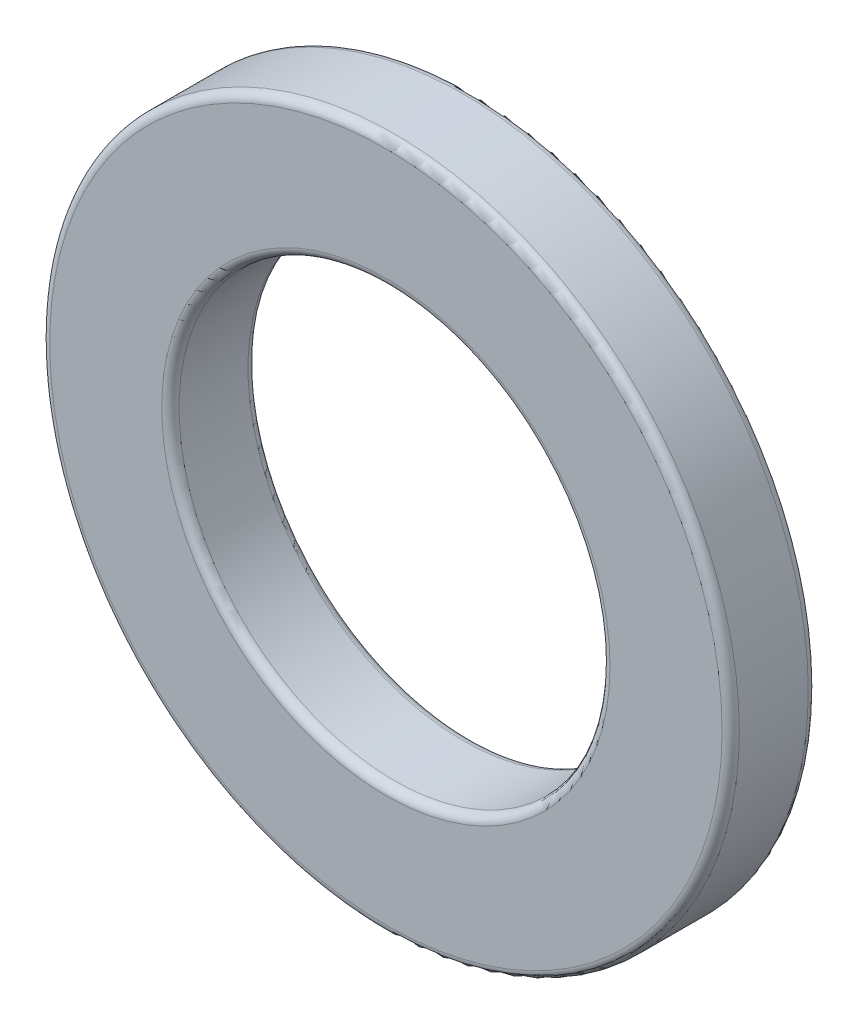
SolidWorks part; units mm, degrees
ref_plane "Front" through (0, 0, 0) normal (0, 0, 1) x (1, 0, 0)
ref_plane "Top" through (0, 0, 0) normal (0, 1, 0) x (1, 0, 0)
ref_plane "Right" through (0, 0, 0) normal (1, 0, 0) x (0, 0, -1)
sketch "Sketch1" plane through (0, 0, 0) normal (0, 0, 1) x (1, 0, 0)
  circle A0 centre (0, 0) radius 2.5
  circle A1 centre (0, 0) radius 4
  dimension "D1" = 8
  dimension "D2" = 5
extrude "Boss-Extrude1" add sketch "Sketch1" along normal blind 1
fillet "Fillet1" radius 0.1 4 edges at (2.5, 0, 0) (4, 0, 0) (2.5, 0, 1) (4, 0, 1)
